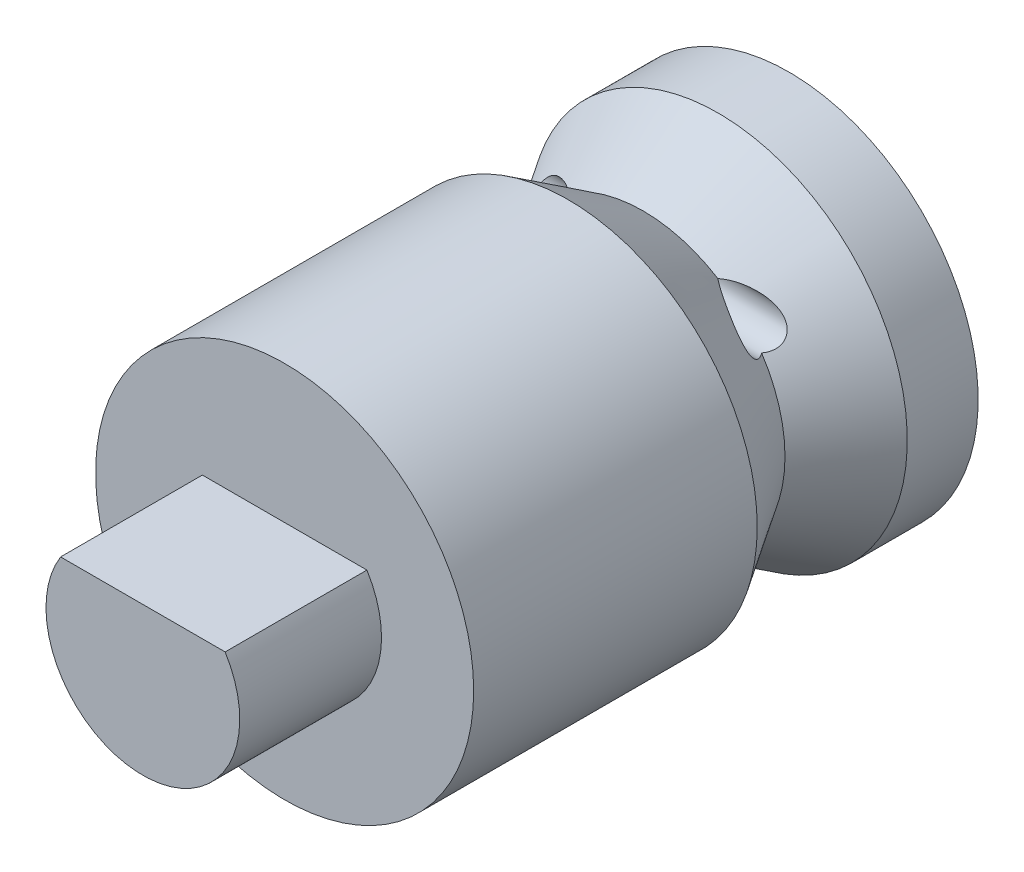
SolidWorks part; units mm, degrees
ref_plane "Front Plane" through (0, 0, 0) normal (0, 0, 1) x (1, 0, 0)
ref_plane "Top Plane" through (0, 0, 0) normal (0, 1, 0) x (1, 0, 0)
ref_plane "Right Plane" through (0, 0, 0) normal (1, 0, 0) x (0, 0, -1)
sketch "Sketch1" plane through (0, 0, 0) normal (0, 0, 1) x (1, 0, 0)
  circle A0 centre (0, 0) radius 4
  dimension "D1" = 8
extrude "Boss-Extrude1" add sketch "Sketch1" along normal blind 3.175
sketch "Sketch2" plane through (0, 0, 3.175) normal (0, 0, 1) x (1, 0, 0)
  line L0 (-1.375, 1.0825) -> (1.375, 1.0825)
  arc A0 (-1.375, 1.0825) -> (1.375, 1.0825) centre (0, 0) ccw
  dimension "D1" = 3.5
  dimension "D2" = 2.75
extrude "Cut-Extrude1" cut sketch "Sketch2" against normal through all
sketch "Sketch3" plane through (0, 0, 0) normal (1, 0, 0) x (0, 0, -1)
  line L0 (-3.175, 4) -> (0, 4)
  line L1 (0, 4) -> (-1.5875, 3)
  line L2 (-1.5875, 3) -> (-3.175, 4)
  point P5 (-1.5875, 4)
  dimension "D1" = 1
ref_axis "Axis1" through (0, 0, 3.175) along (0, 0, -1)
revolve "Cut-Revolve1" cut sketch "Sketch3" angle 360 about axis through (0, 0, 3.175) along (0, 0, -1)
sketch "Sketch4" plane through (0, 0, 3.175) normal (0, 0, 1) x (1, 0, 0)
  circle A7 centre (0, 0) radius 4 construction
  circle A8 centre (0, 0) radius 4
  point P4 (-1.4697, 1.5)
  point P5 (1.4697, 1.5)
extrude "Boss-Extrude2" add sketch "Sketch4" along normal blind 6
sketch "Sketch5" plane through (0, 0, 0) normal (1, 0, 0) x (0, 0, -1)
  line L0 (-1.5875, 3) -> (-1.5875, -3) construction
  line L1 (-1.5875, 3) -> (-1.5875, -3) construction
  circle A0 centre (-1.5875, 2.1) radius 0.45
  dimension "1" = 0.9
  dimension "D1" = 0.9
extrude "Cut-Extrude2" cut sketch "Sketch5" against normal mid plane 8
sketch "Sketch6" plane through (0, 0, 0) normal (0, 0, -1) x (-1, 0, 0)
  circle A1 centre (0, 0) radius 4
  circle A2 centre (0, 0) radius 4
  line M2 (-1.375, 1.0825) -> (1.375, 1.0825)
  arc M3 (1.375, 1.0825) -> (-1.375, 1.0825) centre (0, 0) cw
  circle M4 centre (0, 0) radius 4
  dimension "D1" = 0
extrude "Boss-Extrude3" add sketch "Sketch6" along normal blind 1.5 contours M4 M3 M2
sketch "Sketch7" plane through (0, 0, 9.175) normal (0, 0, 1) x (1, 0, 0)
  line L0 (1.7409, 1.0825) -> (-1.7409, 1.0825)
  arc A0 (-1.375, 1.0825) -> (1.375, 1.0825) centre (0, 0) ccw construction
  arc A1 (-1.375, 1.0825) -> (1.375, 1.0825) centre (0, 0) ccw construction
  arc A2 (-1.7409, 1.0825) -> (1.7409, 1.0825) centre (0, 0) ccw
  arc A4 (-1.6107, 1.2681) -> (1.6107, 1.2681) centre (0, 0) ccw construction
  dimension "D1" = 0.3
extrude "Boss-Extrude4" add sketch "Sketch7" along normal blind 3
sketch "Sketch8" plane through (0, 0, 3.175) normal (0, 0, -1) x (-1, 0, 0)
  line L1 (1.375, 1.0825) -> (-1.375, 1.0825)
  line L2 (1.375, 1.0825) -> (-1.375, 1.0825)
  arc A1 (-1.375, 1.0825) -> (1.375, 1.0825) centre (0, 0) ccw
  arc A2 (-1.375, 1.0825) -> (1.375, 1.0825) centre (0, 0) ccw
  dimension "D1" = 0
extrude "Cut-Extrude3" cut sketch "Sketch8" against normal blind 5
